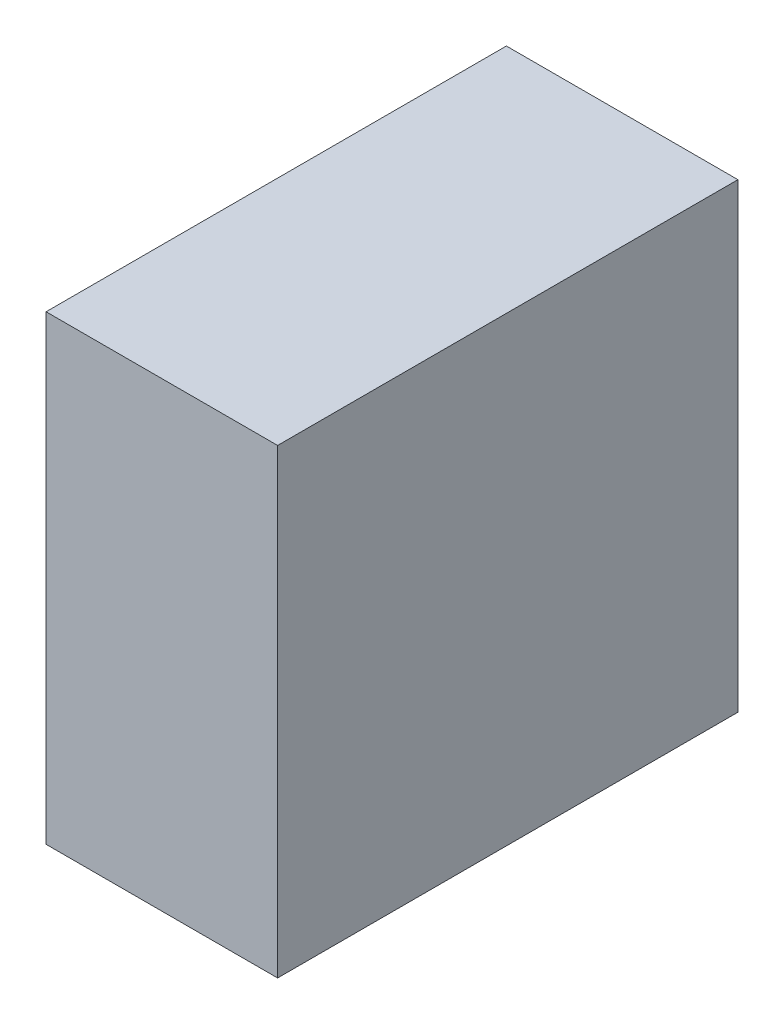
SolidWorks part; units mm, degrees
ref_plane "Plan de face" through (0, 0, 0) normal (0, 0, 1) x (1, 0, 0)
ref_plane "Plan de dessus" through (0, 0, 0) normal (0, 1, 0) x (1, 0, 0)
ref_plane "Plan de droite" through (0, 0, 0) normal (1, 0, 0) x (0, 0, -1)
sketch "Sketch1" plane through (0, 0, 0) normal (0, 0, 1) x (1, 0, 0)
  line L0 (-2, 1002) -> (502, 1002)
  line L1 (0, 0) -> (500, 0)
  line L2 (0, 0) -> (0, 1000)
  line L3 (0, 1000) -> (500, 1000)
  line L4 (500, 0) -> (500, 1000)
  line L5 (502, -2) -> (502, 1002)
  line L6 (-2, -2) -> (502, -2)
  line L7 (-2, -2) -> (-2, 1002)
  dimension "D1" = 500
  dimension "D2" = 1000
  dimension "D3" = 2
extrude "Boss-Extrude1" add sketch "Sketch1" along normal blind 1000
sketch "Sketch2" plane through (0, 0, 1000) normal (0, 0, 1) x (1, 0, 0)
  line L1 (-2, 1002) -> (502, 1002)
  line L2 (-2, 1002) -> (-2, -2)
  line L3 (-2, -2) -> (502, -2)
  line L4 (502, 1002) -> (502, -2)
extrude "Boss-Extrude2" add sketch "Sketch2" along normal blind 2
